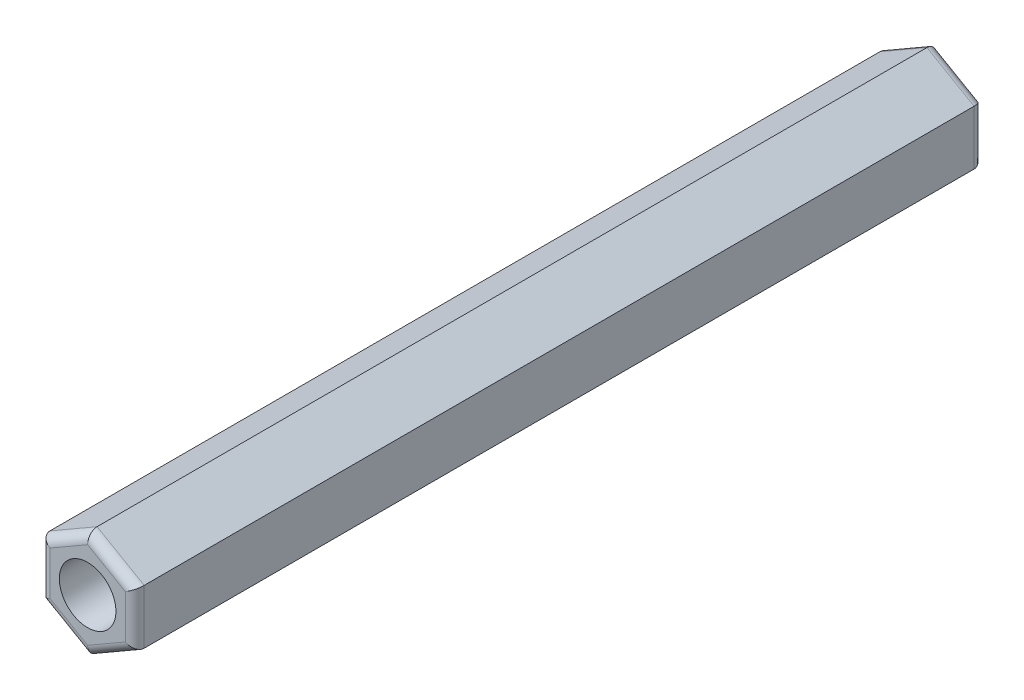
SolidWorks part; units mm, degrees
material "Liga de aço fundido"
ref_plane "Plano frontal" through (0, 0, 0) normal (0, 0, 1) x (1, 0, 0)
ref_plane "Plano superior" through (0, 0, 0) normal (0, 1, 0) x (1, 0, 0)
ref_plane "Plano direito" through (0, 0, 0) normal (1, 0, 0) x (0, 0, -1)
ref_plane "Plano1" through (0, 0, 0) normal (0, 0, -1) x (-1, 0, 0)
sketch "Esboço1" plane through (0, 0, 0) normal (0, 0, -1) x (-1, 0, 0)
  line L0 (67.5021, -1.4434) -> (70.0021, -2.8868)
  line L1 (70.0021, -2.8868) -> (72.5021, -1.4434)
  line L2 (72.5021, -1.4434) -> (72.5021, 1.4434)
  line L3 (72.5021, 1.4434) -> (70.0021, 2.8868)
  line L4 (70.0021, 2.8868) -> (67.5021, 1.4434)
  line L5 (67.5021, 1.4434) -> (67.5021, -1.4434)
extrude "Ressalto-extrusão1" add sketch "Esboço1" against normal blind 45
fillet "Filete1" radius 0.5 12 edges at (-71.2521, 2.1651, 0) (-72.5021, 0, 0) (-68.7521, 2.1651, 0) (-71.2521, -2.1651, 0) (-67.5021, 0, 0) (-68.7521, -2.1651, 0) (-71.2521, 2.1651, 45) (-72.5021, 0, 45) (-68.7521, 2.1651, 45) (-71.2521, -2.1651, 45) (-67.5021, 0, 45) (-68.7521, -2.1651, 45)
sketch "Esboço2" plane through (0, 0, 45) normal (0, 0, 1) x (1, 0, 0)
  circle A0 centre (-70.0021, 0) radius 1.5
  dimension "D1" = 3
extrude "Corte-extrusão1" cut sketch "Esboço2" against normal through all
